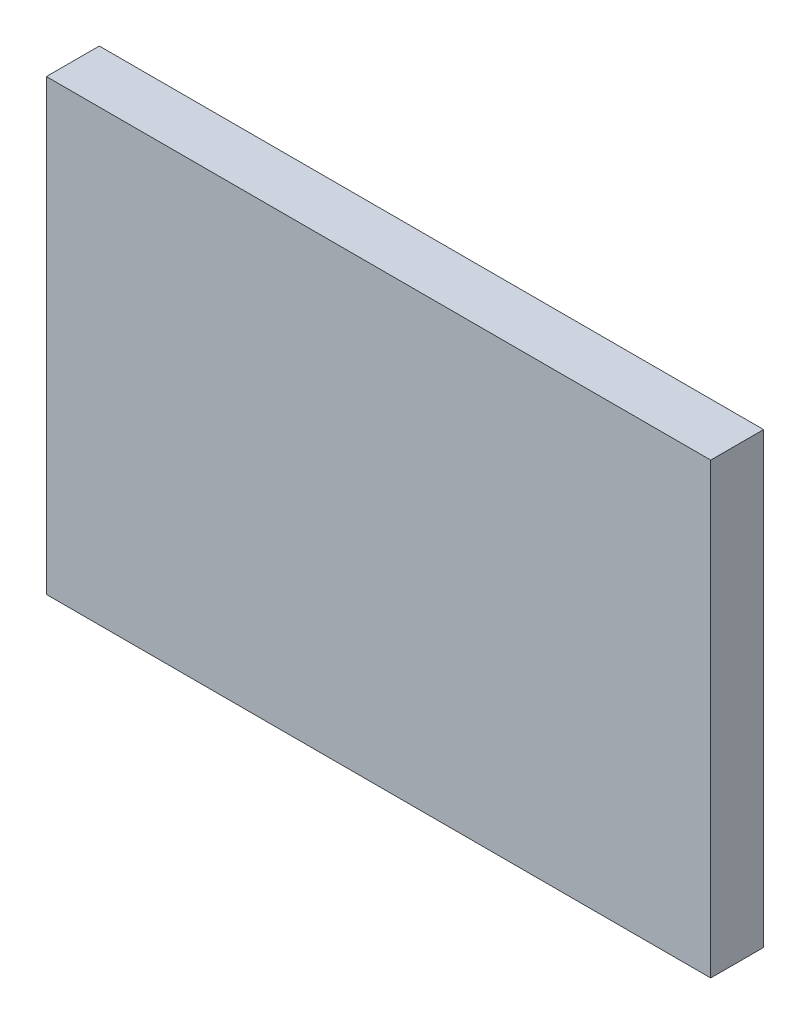
SolidWorks part; units mm, degrees
ref_plane "Front Plane" through (0, 0, 0) normal (0, 0, 1) x (1, 0, 0)
ref_plane "Top Plane" through (0, 0, 0) normal (0, 1, 0) x (1, 0, 0)
ref_plane "Right Plane" through (0, 0, 0) normal (1, 0, 0) x (0, 0, -1)
sketch "Sketch1" plane through (0, 0, 0) normal (0, 0, 1) x (1, 0, 0)
  line L1 (-19.939, -13.462) -> (19.939, -13.462)
  line L2 (-19.939, -13.462) -> (-19.939, 13.462)
  line L3 (-19.939, 13.462) -> (19.939, 13.462)
  line L4 (19.939, -13.462) -> (19.939, 13.462)
  line L5 (-19.939, -13.462) -> (19.939, 13.462) construction
  line L6 (-19.939, 13.462) -> (19.939, -13.462) construction
  point P0 (0, 0)
  dimension "D1" = 26.924
  dimension "D2" = 39.878
extrude "Boss-Extrude1" add sketch "Sketch1" along normal blind 3.175
